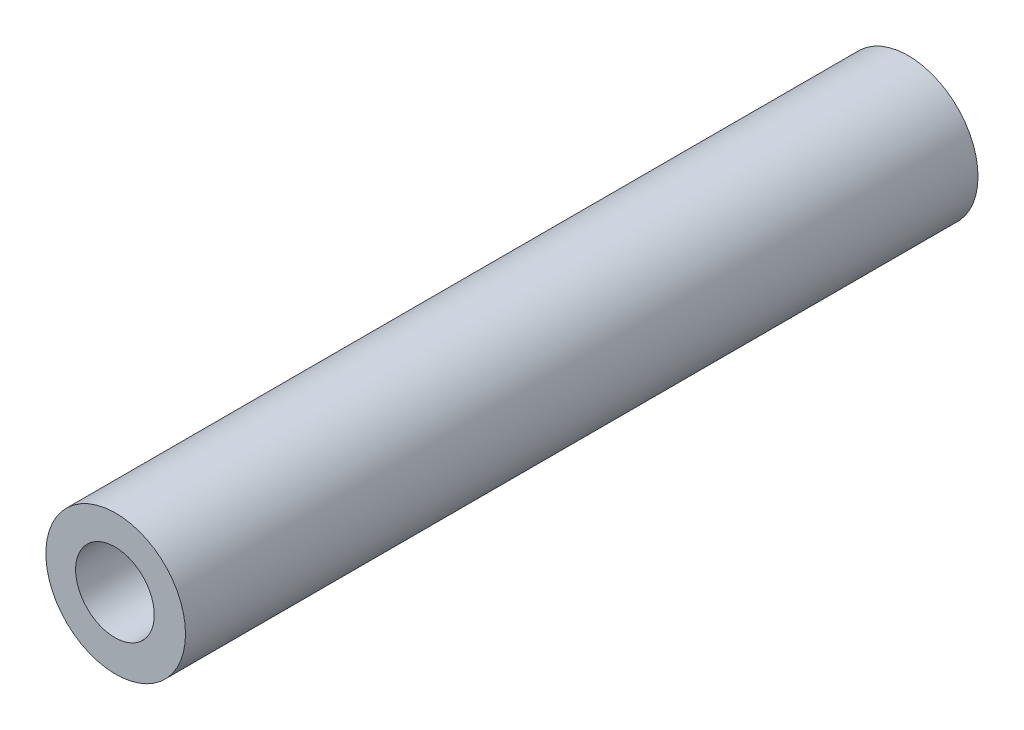
SolidWorks part; units mm, degrees
ref_plane "前视基准面" through (0, 0, 0) normal (0, 0, 1) x (1, 0, 0)
ref_plane "上视基准面" through (0, 0, 0) normal (0, 1, 0) x (1, 0, 0)
ref_plane "右视基准面" through (0, 0, 0) normal (1, 0, 0) x (0, 0, -1)
sketch "草图1" plane through (0, 0, 0) normal (0, 0, 1) x (1, 0, 0)
  circle A0 centre (0.0465, -0.0649) radius 5.815
  circle A1 centre (0.0944, -0.1205) radius 3.265
  dimension "D1" = 11.63
  dimension "D2" = 6.53
extrude "凸台-拉伸2" add sketch "草图1" along normal blind 66 contours A0
sketch "草图5" plane through (0, 0, 66) normal (0, 0, 1) x (1, 0, 0)
  circle A1 centre (-0.0169, 0.0064) radius 3.275
  dimension "D1" = 6.55
extrude "切除-拉伸3" cut sketch "草图5" against normal through all
